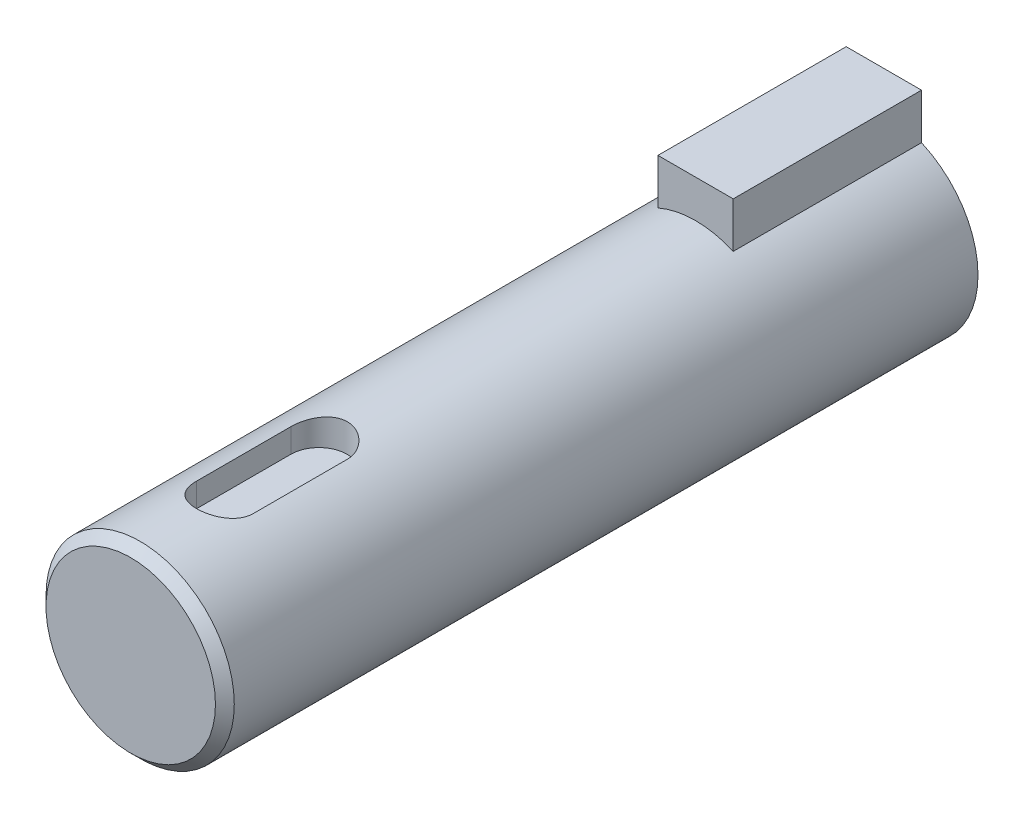
SolidWorks part; units mm, degrees
ref_plane "Front Plane" through (0, 0, 0) normal (0, 0, 1) x (1, 0, 0)
ref_plane "Top Plane" through (0, 0, 0) normal (0, 1, 0) x (1, 0, 0)
ref_plane "Right Plane" through (0, 0, 0) normal (1, 0, 0) x (0, 0, -1)
sketch "Sketch1" plane through (0, 0, 0) normal (0, 0, 1) x (1, 0, 0)
  line L0 (0, 7.1353) -> (0, 7) construction
  line L2 (-2, 7) -> (2, 7)
  line L3 (-2, 7) -> (-2, 4.5826)
  line L5 (2, 7) -> (2, 4.5826)
  arc A0 (-2, 4.5826) -> (2, 4.5826) centre (0, 0) ccw
  point P4 (0, 4.2939)
  dimension "D1" = 10
  dimension "D2" = 4
  dimension "D3" = 7
  dimension "D4" = 4.2939
extrude "Boss-Extrude1" add sketch "Sketch1" along normal blind 10
sketch "Sketch2" plane through (0, 0, 10) normal (0, 0, 1) x (1, 0, 0)
  circle A0 centre (0, 0) radius 5
extrude "Boss-Extrude2" add sketch "Sketch2" along normal blind 30
sketch "Sketch3" plane through (0, 0, 0) normal (0, 1, 0) x (1, 0, 0)
  line L0 (0, -40) -> (0, -17.8015) construction
  line L1 (-5, -40) -> (5, -40) construction
  line L2 (0, -30) -> (0, -35) construction
  line L3 (1.5, -30) -> (1.5, -35)
  line L4 (-1.5, -30) -> (-1.5, -35)
  arc A0 (1.5, -30) -> (-1.5, -30) centre (0, -30) ccw
  arc A1 (-1.5, -35) -> (1.5, -35) centre (0, -35) ccw
  point P7 (0, -32.5)
  point P12 (0, 0)
  dimension "D1" = 3
  dimension "D2" = 5
  dimension "D3" = 5
extrude "Cut-Extrude1" cut sketch "Sketch3" along normal through all from offset 3.5
chamfer "Chamfer1" distance 0.5 angle 45 1 edges at (5, 0, 40)
